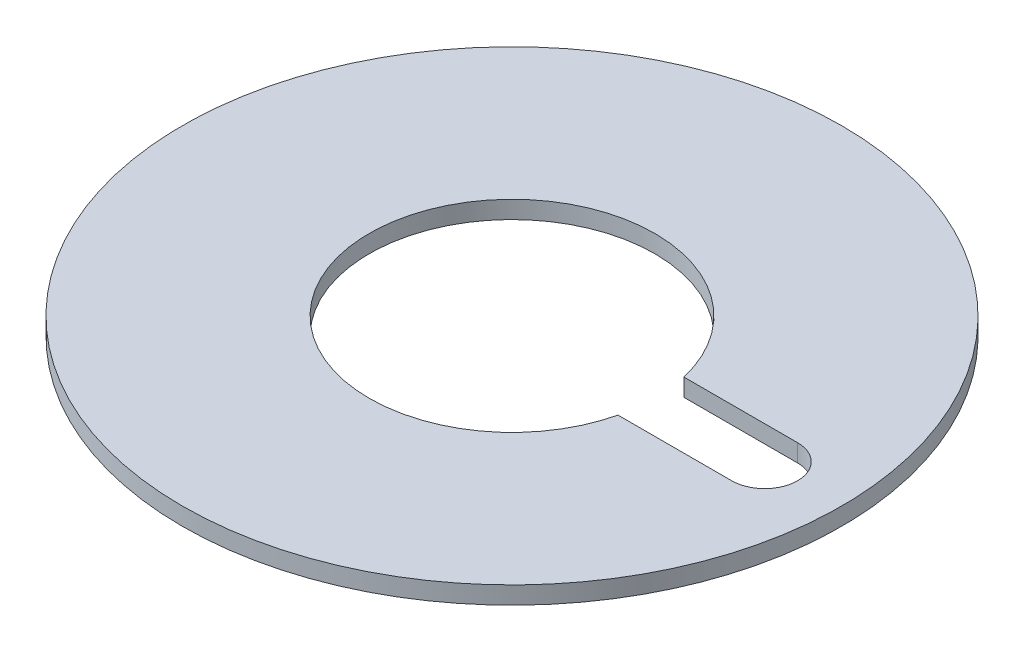
SolidWorks part; units mm, degrees
ref_plane "Front Plane" through (0, 0, 0) normal (0, 0, 1) x (1, 0, 0)
ref_plane "Top Plane" through (0, 0, 0) normal (0, 1, 0) x (1, 0, 0)
ref_plane "Right Plane" through (0, 0, 0) normal (1, 0, 0) x (0, 0, -1)
sketch "Sketch1" plane through (0, 0, 0) normal (0, 1, 0) x (1, 0, 0)
  circle A0 centre (0, 0) radius 15
  dimension "D1" = 30
extrude "Boss-Extrude1" add sketch "Sketch1" along normal blind 0.8
sketch "Sketch3" plane through (0, 0.8, 0) normal (0, 1, 0) x (1, 0, 0)
  line L1 (6.3246, -1.5) -> (11.5, -1.5)
  line L2 (6.3246, 1.5) -> (11.5, 1.5)
  arc A0 (6.3246, 1.5) -> (6.3246, -1.5) centre (0, 0) ccw
  arc A1 (11.5, 1.5) -> (11.5, -1.5) centre (11.5, 0) cw
  point P1 (13, 0)
  point P3 (0, -1.5)
  point P6 (0, 1.5)
  point P8 (0, 0)
  dimension "D1" = 13
  dimension "D2" = 1.5
  dimension "D3" = 1.5
  dimension "D4" = 13
extrude "Cut-Extrude1" cut sketch "Sketch3" against normal through all
